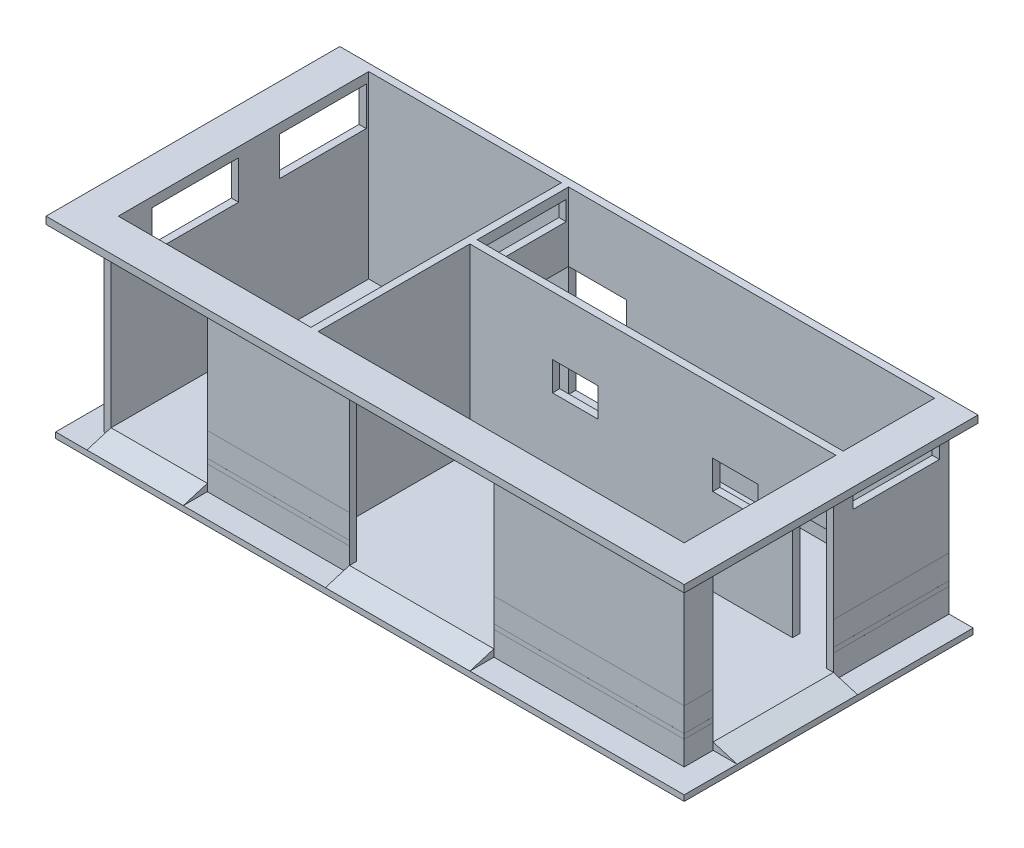
SolidWorks part; units mm, degrees
ref_plane "Alzado" through (0, 0, 0) normal (0, 0, 1) x (1, 0, 0)
ref_plane "Planta" through (0, 0, 0) normal (0, 1, 0) x (1, 0, 0)
ref_plane "Vista lateral" through (0, 0, 0) normal (1, 0, 0) x (0, 0, -1)
sketch "Croquis1" plane through (0, 0, 0) normal (0, 0, 1) x (1, 0, 0)
  line L1 (-3950, -1865) -> (3950, -1865)
  line L2 (-3950, -1865) -> (-3950, 1865)
  line L3 (-3950, 1865) -> (3950, 1865)
  line L4 (3950, -1865) -> (3950, 1865)
  line L5 (-3950, -1865) -> (3950, 1865) construction
  line L6 (-3950, 1865) -> (3950, -1865) construction
  point P0 (0, 0)
  dimension "D1" = 3730
  dimension "D2" = 7900
extrude "Saliente-Extruir1" add sketch "Croquis1" along normal blind 5500
sketch "Croquis2" plane through (0, -1865, 0) normal (0, -1, 0) x (1, 0, 0)
  line L0 (3800, 5350) -> (3800, 150)
  line L1 (-3950, 5500) -> (3950, 5500) construction
  line L2 (-3950, 0) -> (3950, 0) construction
  line L3 (3950, 5500) -> (3950, 0) construction
  line L4 (3800, 5350) -> (-3800, 5350)
  line L5 (-3950, 5500) -> (-3950, 0) construction
  line L6 (3800, 150) -> (-3800, 150)
  line L7 (-3800, 150) -> (-3800, 5350)
  dimension "D1" = 150
  dimension "D2" = 150
  dimension "D3" = 150
  dimension "D4" = 150
extrude "Cortar-Extruir1" cut sketch "Croquis2" against normal blind 3250
sketch "Croquis3" plane through (0, -1865, 0) normal (0, -1, 0) x (1, 0, 0)
  line L0 (-3800, 2050) -> (3800, 2050)
  line L1 (-3800, 5350) -> (-3800, 150) construction
  line L2 (3800, 150) -> (3800, 5350) construction
  line L3 (-3800, 150) -> (3800, 150) construction
  line L4 (3800, 2050) -> (3800, 2200)
  line L5 (3800, 2200) -> (-3800, 2200)
  line L6 (-3800, 5350) -> (-3800, 150) construction
  line L7 (-3800, 2200) -> (-3800, 2050)
  line L8 (3800, 5350) -> (-3800, 5350) construction
  dimension "D1" = 1900
  dimension "D2" = 150
  dimension "D3" = 3150
extrude "Saliente-Extruir2" add sketch "Croquis3" against normal up to surface (3250 mm away) up to face at (0, 1385, 2750)
sketch "Croquis4" plane through (-3950, 0, 0) normal (-1, 0, 0) x (0, 0, 1)
  line L0 (950, -1865) -> (950, 435)
  line L1 (150, -1865) -> (950, -1865)
  line L2 (5500, -1865) -> (0, -1865) construction
  line L3 (950, 435) -> (150, 435)
  line L4 (150, 435) -> (150, -1865)
  dimension "D1" = 800
  dimension "D2" = 2300
extrude "Cortar-Extruir2" cut sketch "Croquis4" against normal blind 150
sketch "Croquis7" plane through (-3950, 0, 0) normal (-1, 0, 0) x (0, 0, 1)
  line L0 (0, 1865) -> (5500, 1865)
  line L1 (5500, 1865) -> (5500, -1865)
  line L2 (5500, -1865) -> (0, -1865)
  line L3 (0, -1865) -> (0, 1865)
extrude "Saliente-Extruir4" add sketch "Croquis7" along normal blind 4150
sketch "Croquis8" plane through (0, -1865, 0) normal (0, -1, 0) x (1, 0, 0)
  line L0 (-3950, 150) -> (-3950, 5350)
  line L1 (-8100, 0) -> (3950, 0) construction
  line L2 (-3800, 5350) -> (-3800, 2200) construction
  line L3 (-7950, 150) -> (-3950, 150)
  line L4 (-8100, 0) -> (-8100, 5500) construction
  line L5 (-7950, 5350) -> (-7950, 150)
  line L6 (-8100, 5500) -> (3950, 5500) construction
  line L7 (-7950, 5350) -> (-3950, 5350)
  dimension "D1" = 150
  dimension "D2" = 150
  dimension "D3" = 150
  dimension "D4" = 150
extrude "Cortar-Extruir3" cut sketch "Croquis8" against normal blind 3250
sketch "Croquis10" plane through (0, -1865, 0) normal (0, -1, 0) x (1, 0, 0)
  line L0 (3800, 2050) -> (2900, 2050)
  line L1 (-3800, 2050) -> (3800, 2050) construction
  line L2 (2900, 2050) -> (2900, 2200)
  line L3 (3800, 2200) -> (-3800, 2200) construction
  line L4 (2900, 2200) -> (3800, 2200)
  line L5 (3800, 2200) -> (3800, 2050)
  dimension "D1" = 900
extrude "Cortar-Extruir5" cut sketch "Croquis10" against normal blind 2300
sketch "Croquis11" plane through (3950, 0, 0) normal (1, 0, 0) x (0, 0, -1)
  line L0 (-5500, -1865) -> (-5500, 1865) construction
  line L1 (-5500, -1865) -> (0, -1865) construction
  line L2 (-4900, 1535) -> (-2400, 1535)
  line L3 (-2400, 1535) -> (-2400, -1865)
  line L4 (-2400, -1865) -> (-4900, -1865)
  line L5 (-4900, 1535) -> (-4900, -1865)
  dimension "D1" = 600
  dimension "D2" = 2500
  dimension "D3" = 3400
extrude "Cortar-Extruir6" cut sketch "Croquis11" against normal blind 150
sketch "Croquis12" plane through (3950, 0, 0) normal (1, 0, 0) x (0, 0, -1)
  line L1 (0, -1865) -> (0, 1865) construction
  line L2 (-5500, 1865) -> (0, 1865) construction
  line L3 (-2000, 1665) -> (-2000, 865)
  line L4 (-2000, 865) -> (-200, 865)
  line L5 (-2000, 1665) -> (-200, 1665)
  line L6 (-200, 1665) -> (-200, 865)
  point P7 (-200, 1265)
  dimension "D1" = 1800
  dimension "D2" = 1000
  dimension "D3" = 200
  dimension "D4" = 200
  dimension "D6" = 200
extrude "Cortar-Extruir7" cut sketch "Croquis12" against normal blind 150
sketch "Croquis13" plane through (0, 0, 5500) normal (0, 0, 1) x (1, 0, 0)
  line L0 (-3800, -1865) -> (-3000, -1865)
  line L1 (-8100, -1865) -> (3950, -1865) construction
  line L2 (-3000, -1865) -> (0, -1865)
  line L3 (-3000, -1865) -> (-3000, 1535)
  line L4 (-3000, 1535) -> (0, 1535)
  line L5 (0, 1535) -> (0, -1865)
  line M7 (-8100, -1865) -> (3950, -1865)
  dimension "D1" = 800
  dimension "D2" = 3000
  dimension "D3" = 3400
extrude "Cortar-Extruir8" cut sketch "Croquis13" against normal blind 150 contours L5 L4 L3 M7
sketch "Croquis15" plane through (-8100, 0, 0) normal (-1, 0, 0) x (0, 0, 1)
  line L0 (200, 1665) -> (2000, 1665)
  line L1 (0, 1865) -> (0, -1865) construction
  line L2 (200, 865) -> (2000, 865)
  line L3 (2000, 865) -> (2000, 1665)
  line L6 (200, 1665) -> (200, 865)
  dimension "D1" = 1800
  dimension "D4" = 200
extrude "Cortar-Extruir10" cut sketch "Croquis15" against normal blind 150
sketch "Croquis16" plane through (0, 0, 0) normal (0, 0, -1) x (-1, 0, 0)
  line L0 (8100, 1865) -> (8100, -1865) construction
  line L2 (4950, 435) -> (4950, -1865)
  line L3 (6950, 435) -> (4950, 435)
  line L4 (8100, -1865) -> (-3950, -1865) construction
  line L5 (6950, 435) -> (6950, -1865)
  line L7 (6950, -1865) -> (4950, -1865)
  dimension "D1" = 1150
  dimension "D2" = 2000
  dimension "D3" = 2300
extrude "Cortar-Extruir11" cut sketch "Croquis16" against normal blind 150
sketch "Croquis17" plane through (0, 0, 5500) normal (0, 0, 1) x (1, 0, 0)
  line L0 (-8100, 1865) -> (-8100, 1715)
  line L1 (-8100, -1865) -> (-8100, 1865) construction
  line L2 (-8100, 1715) -> (3950, 1715)
  line L3 (-8100, 1865) -> (3950, 1865)
  line L4 (3950, 1865) -> (3950, 1715)
  line L5 (3950, -1865) -> (3950, 1865) construction
  dimension "D1" = 150
extrude "Saliente-Extruir5" add sketch "Croquis17" along normal blind 600
sketch "Croquis18" plane through (3950, 0, 0) normal (1, 0, 0) x (0, 0, -1)
  line L0 (-6100, 1865) -> (0, 1865)
  line L1 (-6100, 1715) -> (-6100, 1865)
  line L3 (-6100, 1715) -> (0, 1715)
  line L4 (0, -1865) -> (0, 1865) construction
  line L5 (0, 1715) -> (0, 1865)
extrude "Saliente-Extruir6" add sketch "Croquis18" along normal blind 600
sketch "Croquis19" plane through (-8100, 0, 0) normal (-1, 0, 0) x (0, 0, 1)
  line L0 (0, 1865) -> (6100, 1865)
  line L1 (6100, 1865) -> (6100, 1715)
  line L2 (6100, 1715) -> (0, 1715)
  line L3 (0, 1715) -> (0, 1865)
extrude "Saliente-Extruir7" add sketch "Croquis19" along normal blind 600
sketch "Croquis20" plane through (0, 1385, 0) normal (0, -1, 0) x (1, 0, 0)
  line L0 (3800, 150) -> (3800, 2050)
  line L1 (3800, 2050) -> (-3800, 2050)
  line L2 (-3800, 2050) -> (-3800, 150)
  line L3 (-3800, 150) -> (3800, 150)
  line L4 (3800, 2200) -> (-3800, 2200)
  line L5 (-3800, 2200) -> (-3800, 5350)
  line L6 (-3800, 5350) -> (3800, 5350)
  line L7 (3800, 5350) -> (3800, 2200)
  line L8 (-3950, 150) -> (-7950, 150)
  line L9 (-7950, 150) -> (-7950, 5350)
  line L10 (-7950, 5350) -> (-3950, 5350)
  line L11 (-3950, 150) -> (-3950, 5350) construction
  line L12 (-3950, 950) -> (-3950, 5350) construction
  line L13 (-3950, 5350) -> (-3950, 150)
extrude "Cortar-Extruir12" cut sketch "Croquis20" against normal blind 1280
sketch "Croquis21" plane through (0, 0, 5500) normal (0, 0, 1) x (1, 0, 0)
  line L0 (-7950, -1865) -> (-5950, -1865)
  line L1 (-8100, -1865) -> (-3000, -1865) construction
  line L2 (-5950, -1865) -> (-5950, 1535)
  line L3 (-5950, 1535) -> (-7950, 1535)
  line L7 (-7950, -1865) -> (-7950, 1535)
  dimension "D2" = 3400
extrude "Cortar-Extruir13" cut sketch "Croquis21" against normal up to surface (150 mm away) up to face at (-5950, 0, 5350)
sketch "Croquis24" plane through (0, 0, 0) normal (0, 0, -1) x (-1, 0, 0)
  line L0 (4950, 435) -> (6950, 435)
  line L1 (6950, 435) -> (6950, -1865)
  line L2 (6950, -1865) -> (4950, -1865)
  line L3 (3950, -1865) -> (5950, -1865) construction
  line L4 (4950, -1865) -> (4950, 435)
extrude "Saliente-Extruir11" add sketch "Croquis24" against normal blind 150
sketch "Croquis25" plane through (-3800, 0, 0) normal (1, 0, 0) x (0, 0, -1)
  line L0 (-2000, 1665) -> (-2000, 1265)
  line L1 (-2000, 1665) -> (-2000, 865) construction
  line L3 (-2000, 1265) -> (-200, 1265)
  line L5 (-200, 865) -> (-200, 1665) construction
  line L7 (-200, 1265) -> (-200, 1665)
  line L8 (-200, 1665) -> (-2000, 1665)
extrude "Cortar-Extruir14" cut sketch "Croquis25" against normal blind 170
sketch "Croquis26" plane through (0, -1865, 0) normal (0, -1, 0) x (1, 0, 0)
  line L0 (-8100, 5500) -> (3950, 5500)
  line L1 (3950, 5500) -> (3950, 0)
  line L2 (3950, 0) -> (-8100, 0)
  line L3 (-8100, 0) -> (-8100, 5500)
extrude "Saliente-Extruir12" add sketch "Croquis26" along normal blind 270
sketch "Croquis27" plane through (0, -2135, 0) normal (0, -1, 0) x (1, 0, 0)
  line L0 (-8100, 0) -> (-8100, 5500)
  line L1 (3950, 5500) -> (-8100, 5500) construction
  line L2 (-8100, 5500) -> (-8100, 0) construction
  line L3 (-8100, 5500) -> (3950, 5500)
  line L4 (3950, 5500) -> (3950, 0)
  line L5 (-8600, 0) -> (-8600, 6000)
  line L6 (-8600, 6000) -> (4450, 6000)
  line L7 (4450, 6000) -> (4450, 0)
  line L8 (-8600, 0) -> (-8100, 0)
  line L9 (3950, 0) -> (4450, 0)
  dimension "D1" = 500
extrude "Saliente-Extruir13" add sketch "Croquis27" against normal blind 120 separate body
sketch "Croquis33" plane through (3950, 0, 0) normal (1, 0, 0) x (0, 0, -1)
  line L0 (-4900, -1865) -> (-4900, -2015)
  line L1 (0, -2015) -> (-6000, -2015) construction
  line L2 (-4900, -2015) -> (-2400, -2015)
  line L3 (-2400, -2015) -> (-2400, -1865)
  line L4 (-2400, -1865) -> (-4900, -1865)
extrude "Saliente-Extruir19" add sketch "Croquis33" along normal blind 500
sketch "Croquis34" plane through (0, 0, 5500) normal (0, 0, 1) x (1, 0, 0)
  line L0 (-7950, -1865) -> (-7950, -2015)
  line L1 (-8100, -2015) -> (3950, -2015) construction
  line L2 (-7950, -2015) -> (-5950, -2015)
  line L3 (4450, -2015) -> (-8600, -2015) construction
  line L4 (-5950, -2015) -> (-5950, -1865)
  line L5 (-5950, -1865) -> (-7950, -1865)
  line L6 (-3000, -1865) -> (-3000, -2015)
  line L7 (-3000, -2015) -> (0, -2015)
  line L8 (0, -2015) -> (0, -1865)
  line L9 (0, -1865) -> (-3000, -1865)
extrude "Saliente-Extruir20" add sketch "Croquis34" along normal blind 500
sketch "Croquis35" plane through (-7950, 0, 0) normal (-1, 0, 0) x (0, 0, 1)
  line L0 (6000, -2015) -> (5500, -1865)
  line L1 (5500, -1865) -> (6000, -1865)
  line L2 (6000, -1865) -> (6000, -2015) construction
  line L3 (6000, -1865) -> (5500, -1865) construction
  line L4 (6000, -1865) -> (6000, -2015)
extrude "Cortar-Extruir15" cut sketch "Croquis35" against normal up to surface (7950 mm away) up to face at (0, -1940, 5750)
sketch "Croquis36" plane through (0, 0, 2400) normal (0, 0, -1) x (-1, 0, 0)
  line L0 (-4450, -1865) -> (-3950, -1865)
  line L1 (-3950, -1865) -> (-4450, -2015)
  line L2 (-4450, -2015) -> (-4450, -1865)
extrude "Cortar-Extruir16" cut sketch "Croquis36" against normal blind 2500
sketch "Croquis37" plane through (-8100, 0, 0) normal (-1, 0, 0) x (0, 0, 1)
  line L0 (0, -1515) -> (5500, -1515)
  line L1 (0, 1715) -> (0, -2015) construction
  line L2 (5500, -2015) -> (5500, 1715) construction
  line L3 (5500, -1515) -> (5500, -2015)
  line L4 (5500, -2015) -> (0, -2015)
  line L5 (0, -2015) -> (5500, -2015) construction
  line L6 (0, -2015) -> (0, -2135) construction
  line L7 (0, -1515) -> (0, -2015)
  dimension "D1" = 500
extrude "Cortar-Extruir17" cut sketch "Croquis37" against normal blind 0.1
sketch "Croquis38" plane through (0, 0, 5500) normal (0, 0, 1) x (1, 0, 0)
  line L0 (-5950, -2015) -> (-5950, -1515)
  line L1 (-5950, -1865) -> (-5950, 1535) construction
  line L2 (-5950, -1515) -> (-3000, -1515)
  line L3 (-3000, -1865) -> (-3000, 1535) construction
  line L4 (-3000, -1515) -> (-3000, -2015)
  line L5 (-3000, -2015) -> (-5950, -2015)
  line L6 (0, -1515) -> (3950, -1515)
  line L7 (0, 1535) -> (0, -1865) construction
  line L8 (3950, -2015) -> (3950, 1715) construction
  line L9 (3950, -1515) -> (3950, -2015)
  line L10 (3950, -2015) -> (0, -2015)
  line L11 (0, -2015) -> (0, -1515)
  dimension "D1" = 500
extrude "Cortar-Extruir18" cut sketch "Croquis38" against normal blind 0.1
sketch "Croquis40" plane through (3950, 0, 0) normal (1, 0, 0) x (0, 0, -1)
  line L0 (-2400, -2015) -> (-2400, -1515)
  line L1 (-2400, -1865) -> (-2400, 1535) construction
  line L2 (-2400, -1515) -> (0, -1515)
  line L3 (0, -2015) -> (0, 1715) construction
  line L4 (0, -1515) -> (0, -2015)
  line L5 (0, -2015) -> (-2400, -2015)
  line L6 (-4900, -2015) -> (-4900, -1515)
  line L7 (-4900, 1535) -> (-4900, -1865) construction
  line L8 (-4900, -1515) -> (-5500, -1515)
  line L9 (-5500, -1515) -> (-5500, 1715) construction
  line L10 (-5500, -1515) -> (-5499.9, -2015)
  line L11 (-5499.9, -2015) -> (-4900, -2015)
  dimension "D1" = 500
  dimension "D2" = 500
extrude "Cortar-Extruir21" cut sketch "Croquis40" against normal blind 0.1
sketch "Croquis42" plane through (-8100, 0, 0) normal (-1, 0, 0) x (0, 0, 1)
  line L0 (0, 1715) -> (0, -1515) construction
  line L1 (0, -556.1987) -> (5500, -556.1987)
  line L2 (0, -556.1987) -> (0, -1415)
  line L3 (0, -1415) -> (5500, -1415)
  line L4 (5500, -556.1987) -> (5500, -1415)
  line L5 (0, -556.1987) -> (5500, -1415) construction
  line L6 (0, -1415) -> (5500, -556.1987) construction
  line L7 (5500, -1515) -> (5500, 1715) construction
  line L8 (5500, -1515) -> (0, -1515) construction
  point P0 (2750, -985.5994)
  dimension "D1" = 100
extrude "Cortar-Extruir24" cut sketch "Croquis42" against normal blind 0.1
sketch "Croquis43" plane through (0, 0, 5500) normal (0, 0, 1) x (1, 0, 0)
  line L0 (-3000, -1515) -> (-3000, 1535) construction
  line L1 (-5950, -915) -> (-3000, -915)
  line L2 (-5950, -915) -> (-5950, -1415)
  line L3 (-5950, -1415) -> (-3000, -1415)
  line L4 (-3000, -915) -> (-3000, -1415)
  line L5 (-5950, -915) -> (-3000, -1415) construction
  line L6 (-5950, -1415) -> (-3000, -915) construction
  line L7 (-5950, -1515) -> (-5950, 1535) construction
  line L8 (-3000, -1515) -> (-5950, -1515) construction
  line L9 (3950, -1515) -> (3950, 1715) construction
  line L10 (0, -915) -> (3950, -915)
  line L11 (0, -915) -> (0, -1415)
  line L12 (0, -1415) -> (3950, -1415)
  line L13 (3950, -915) -> (3950, -1415)
  line L14 (0, -915) -> (3950, -1415) construction
  line L15 (0, -1415) -> (3950, -915) construction
  line L16 (0, 1535) -> (0, -1515) construction
  line L17 (3950, -1515) -> (0, -1515) construction
  point P0 (-4475, -1165)
  point P12 (1975, -1165)
  dimension "D1" = 100
  dimension "D2" = 500
  dimension "D3" = 100
  dimension "D4" = 500
extrude "Cortar-Extruir25" cut sketch "Croquis43" against normal blind 0.1
sketch "Croquis44" plane through (3950, 0, 0) normal (1, 0, 0) x (0, 0, -1)
  line L0 (-4900, 1535) -> (-4900, -1515) construction
  line L1 (-5499.9, -915) -> (-4900, -915)
  line L2 (-5499.9, -915) -> (-5499.9, -1415)
  line L3 (-5499.9, -1415) -> (-4900, -1415)
  line L4 (-4900, -915) -> (-4900, -1415)
  line L5 (-5499.9, -915) -> (-4900, -1415) construction
  line L6 (-5499.9, -1415) -> (-4900, -915) construction
  line L7 (-5499.9, -1415) -> (-5499.9, -915) construction
  line L8 (-4900, -1515) -> (-5499.9, -1515) construction
  line L9 (-2400, -1515) -> (-2400, 1535) construction
  line L10 (-2400, -915) -> (0, -915)
  line L11 (-2400, -915) -> (-2400, -1415)
  line L12 (-2400, -1415) -> (0, -1415)
  line L13 (0, -915) -> (0, -1415)
  line L14 (-2400, -915) -> (0, -1415) construction
  line L15 (-2400, -1415) -> (0, -915) construction
  point P0 (-5199.95, -1165)
  point P12 (-1200, -1165)
  dimension "D1" = 100
  dimension "D2" = 500
  dimension "D3" = 500
extrude "Cortar-Extruir26" cut sketch "Croquis44" against normal blind 0.1
sketch "Croquis47" plane through (0, 0, 0) normal (0, 0, -1) x (-1, 0, 0)
  line L0 (3800, -1865) -> (3800, 435)
  line L2 (3800, 1865) -> (3800, 435) construction
  line L4 (3800, 435) -> (2600, 435)
  line L5 (2600, 435) -> (2600, -1865)
  line L6 (7950, -1865) -> (-3800, -1865) construction
  line L7 (2600, -1865) -> (3800, -1865)
  dimension "D1" = 2300
  dimension "D2" = 1200
extrude "Cortar-Extruir28" cut sketch "Croquis47" against normal up to surface (150 mm away) up to face at (-2975, 575, 150)
sketch "Croquis48" plane through (-8100, 0, 0) normal (-1, 0, 0) x (0, 0, 1)
  line L0 (2850, 865) -> (4650, 865)
  line L1 (4650, 865) -> (4650, 1665)
  line L2 (2850, 865) -> (2850, 1665)
  line L3 (2850, 1665) -> (4650, 1665)
  line L4 (5500, -556.1987) -> (5500, 1715) construction
  line L6 (0, 1715) -> (5500, 1715) construction
  dimension "D1" = 850
  dimension "D2" = 50
  dimension "D3" = 800
  dimension "D4" = 1800
extrude "Cortar-Extruir29" cut sketch "Croquis48" against normal up to surface (150 mm away) up to face at (-7950, 1265, 1100)
sketch "Croquis50" plane through (0, 0, 2200) normal (0, 0, 1) x (1, 0, 0)
  line L0 (-2084, 645) -> (-2084, 45)
  line L1 (-2084, 45) -> (-1140, 45)
  line L2 (-1140, 45) -> (-1140, 645)
  line L3 (-1140, 645) -> (-2084, 645)
  line L4 (0, -1865) -> (-3000, -1865) construction
  line L5 (-3800, 1865) -> (-3800, -1865) construction
  line L6 (3800, -1865) -> (0, -1865) construction
  line L7 (1242, -65) -> (2186, -65)
  line L8 (1242, -65) -> (1242, 535)
  line L9 (1242, 535) -> (2186, 535)
  line L10 (2186, -65) -> (2186, 535)
  line L11 (1242, -65) -> (2186, 535) construction
  line L12 (1242, 535) -> (2186, -65) construction
  point P8 (-1612, 645)
  point P9 (1714, 235)
  point P16 (1714, 535)
  dimension "D1" = 1910
  dimension "D2" = 944
  dimension "D3" = 600
  dimension "D4" = 2188
  dimension "D5" = 944
  dimension "D6" = 600
  dimension "D7" = 1800
  dimension "D8" = 2854
extrude "Cortar-Extruir30" cut sketch "Croquis50" against normal up to surface (150 mm away) up to face at (966.6667, 145, 2050)
